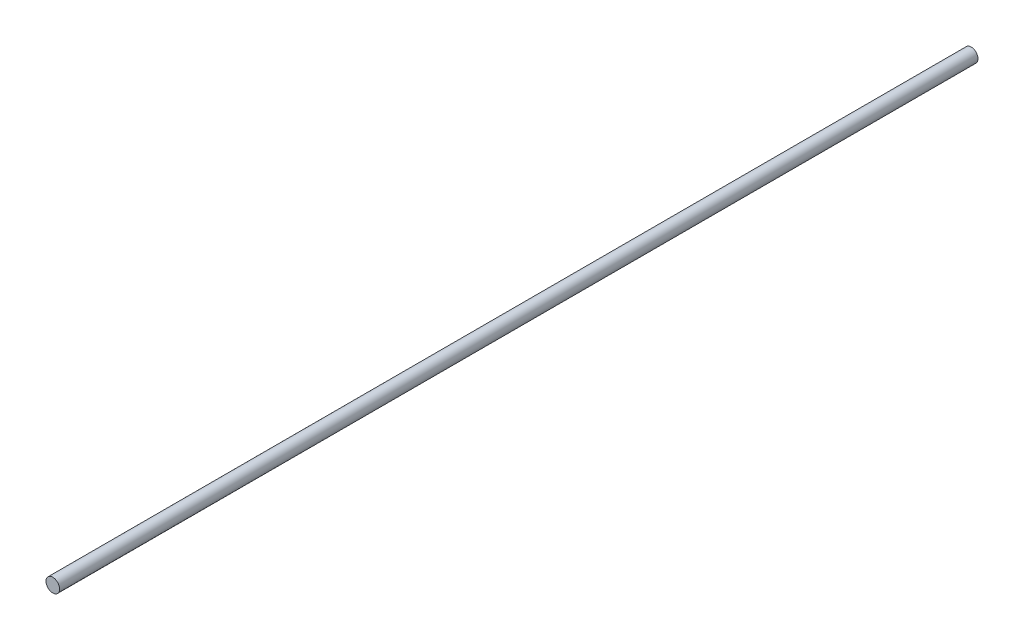
SolidWorks part; units mm, degrees
material "Plain Carbon Steel"
ref_plane "Front Plane" through (0, 0, 0) normal (0, 0, 1) x (1, 0, 0)
ref_plane "Top Plane" through (0, 0, 0) normal (0, 1, 0) x (1, 0, 0)
ref_plane "Right Plane" through (0, 0, 0) normal (1, 0, 0) x (0, 0, -1)
sketch "Sketch1" plane through (0, 0, 0) normal (0, 0, 1) x (1, 0, 0)
  circle A0 centre (0, 0) radius 4
  dimension "D1" = 8
extrude "Boss-Extrude1" add sketch "Sketch1" along normal blind 540
